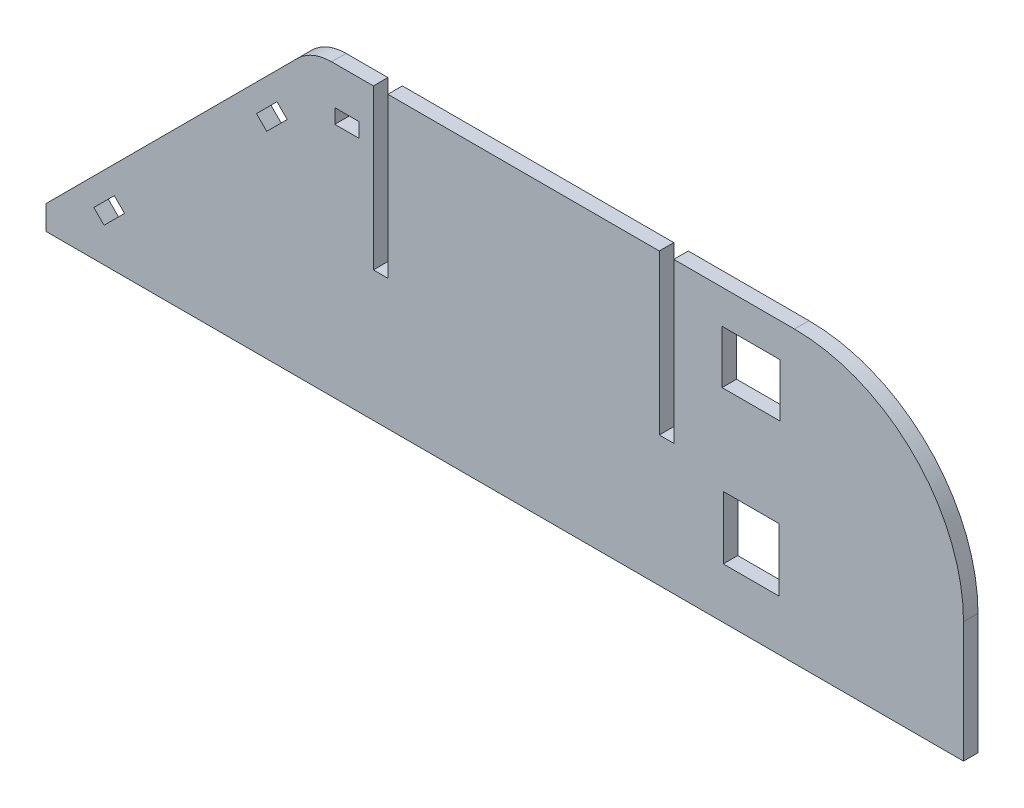
SolidWorks part; units mm, degrees
ref_plane "Alzado" through (0, 0, 0) normal (0, 0, 1) x (1, 0, 0)
ref_plane "Planta" through (0, 0, 0) normal (0, 1, 0) x (1, 0, 0)
ref_plane "Vista lateral" through (0, 0, 0) normal (1, 0, 0) x (0, 0, -1)
sketch "Croquis1" plane through (0, 0, 0) normal (0, 0, 1) x (1, 0, 0)
  line L0 (0, 30) -> (0, -30) construction
  line L1 (-95, 30) -> (95, 30)
  line L2 (-95, 30) -> (-95, -30)
  line L3 (-95, -30) -> (95, -30)
  line L4 (95, 30) -> (95, -30)
  line L5 (-95, 30) -> (95, -30) construction
  line L6 (-95, -30) -> (95, 30) construction
  line L7 (-40, 30) -> (-95, -25)
  line L10 (-21.5, -30) -> (-18.5, -30)
  line L11 (-21.5, 30) -> (-18.5, 30)
  point P0 (0, 0)
  point P8 (0, -22.5)
  point P13 (0, 22.5)
  dimension "D1" = 60
  dimension "D2" = 190
  dimension "D3" = 5
  dimension "D4" = 55
extrude "Saliente-Extruir1" add sketch "Croquis1" along normal blind 3
fillet "Redondeo1" radius 35 1 edges at (95, 30, 1.5)
sketch "Croquis2" plane through (0, 0, 3) normal (0, 0, 1) x (1, 0, 0)
  line L0 (-40, 30) -> (60, 30) construction
  line L1 (35, 30) -> (32, 30)
  line L2 (35, 30) -> (35, -3)
  line L3 (35, -3) -> (32, -3)
  line L4 (32, 30) -> (32, -3)
  line L5 (10, 30) -> (10, -30) construction
  line L6 (-27.2, 30) -> (-24.2, 30)
  line L7 (-27.2, 30) -> (-27.2, -3)
  line L8 (-27.2, -3) -> (-24.2, -3)
  line L9 (-24.2, 30) -> (-24.2, -3)
  line L10 (-95, -30) -> (95, -30) construction
  line L11 (95, -5) -> (95, -30) construction
  dimension "D1" = 33
  dimension "D2" = 33
  dimension "D3" = 3
  dimension "D4" = 3
  dimension "D5" = 56.2
  dimension "D6" = 60
extrude "Cortar-Extruir1" cut sketch "Croquis2" against normal through all
sketch "Croquis3" plane through (0, 0, 0) normal (0, 0, -1) x (-1, 0, 0)
  line L0 (95, -30) -> (-95, -30) construction
  line L1 (-56.75, -6.5) -> (-45.25, -6.5)
  line L2 (-56.75, -6.5) -> (-56.75, -19.5)
  line L3 (-56.75, -19.5) -> (-45.25, -19.5)
  line L4 (-45.25, -6.5) -> (-45.25, -19.5)
  line L5 (-56.75, -6.5) -> (-45.25, -19.5) construction
  line L6 (-56.75, -19.5) -> (-45.25, -6.5) construction
  line L7 (-95, -5) -> (-95, -30) construction
  point P0 (-51, -13)
  dimension "D1" = 11.5
  dimension "D2" = 13
  dimension "D3" = 10.5
  dimension "D4" = 44
extrude "Cortar-Extruir2" cut sketch "Croquis3" against normal through all
sketch "Croquis4" plane through (0, 0, 0) normal (0, 0, -1) x (-1, 0, 0)
  line L0 (-95, -5) -> (-95, -30) construction
  line L1 (-57, 23) -> (-45, 23)
  line L2 (-57, 23) -> (-57, 12)
  line L3 (-57, 12) -> (-45, 12)
  line L4 (-45, 23) -> (-45, 12)
  line L5 (-57, 23) -> (-45, 12) construction
  line L6 (-57, 12) -> (-45, 23) construction
  line L7 (-35, 30) -> (-60, 30) construction
  point P0 (-51, 17.5)
  dimension "D1" = 12
  dimension "D2" = 11
  dimension "D3" = 44
  dimension "D4" = 12.5
extrude "Cortar-Extruir3" cut sketch "Croquis4" against normal through all
fillet "Redondeo2" radius 10 1 edges at (-40, 30, 1.5)
sketch "Croquis5" plane through (0, 0, 0) normal (0, 0, -1) x (-1, 0, 0)
  line L0 (42.9289, 27.0711) -> (35.8759, 20.018) construction
  line L1 (47.1716, 17.1716) -> (45.0503, 15.0503)
  line L2 (45.0503, 15.0503) -> (49.2929, 10.8076)
  line L3 (49.2929, 10.8076) -> (51.4142, 12.9289)
  line L4 (51.4142, 12.9289) -> (47.1716, 17.1716)
  line L5 (95, -25) -> (90, -30) construction
  line L7 (85.1005, -20.7574) -> (82.9792, -22.8787)
  line L8 (82.9792, -22.8787) -> (78.7365, -18.636)
  line L9 (78.7365, -18.636) -> (80.8579, -16.5147)
  line L10 (80.8579, -16.5147) -> (85.1005, -20.7574)
  line L11 (42.9289, 27.0711) -> (95, -25) construction
  dimension "D1" = 6
  dimension "D2" = 3
  dimension "D3" = 10
  dimension "D4" = 4
  dimension "D5" = 3
  dimension "D6" = 6
  dimension "D7" = 10
  dimension "D8" = 4
extrude "Cortar-Extruir4" cut sketch "Croquis5" against normal through all
sketch "Croquis6" plane through (0, 0, 0) normal (0, 0, -1) x (-1, 0, 0)
  line L0 (35.8579, 30) -> (27.2, 30) construction
  line L1 (30.2, 22.11) -> (35.2, 22.11)
  line L2 (30.2, 22.11) -> (30.2, 19.11)
  line L3 (30.2, 19.11) -> (35.2, 19.11)
  line L4 (35.2, 22.11) -> (35.2, 19.11)
  line L5 (27.2, 30) -> (27.2, -3) construction
  dimension "D1" = 5
  dimension "D2" = 3
  dimension "D3" = 7.89
  dimension "D4" = 3
extrude "Cortar-Extruir5" cut sketch "Croquis6" against normal through all
